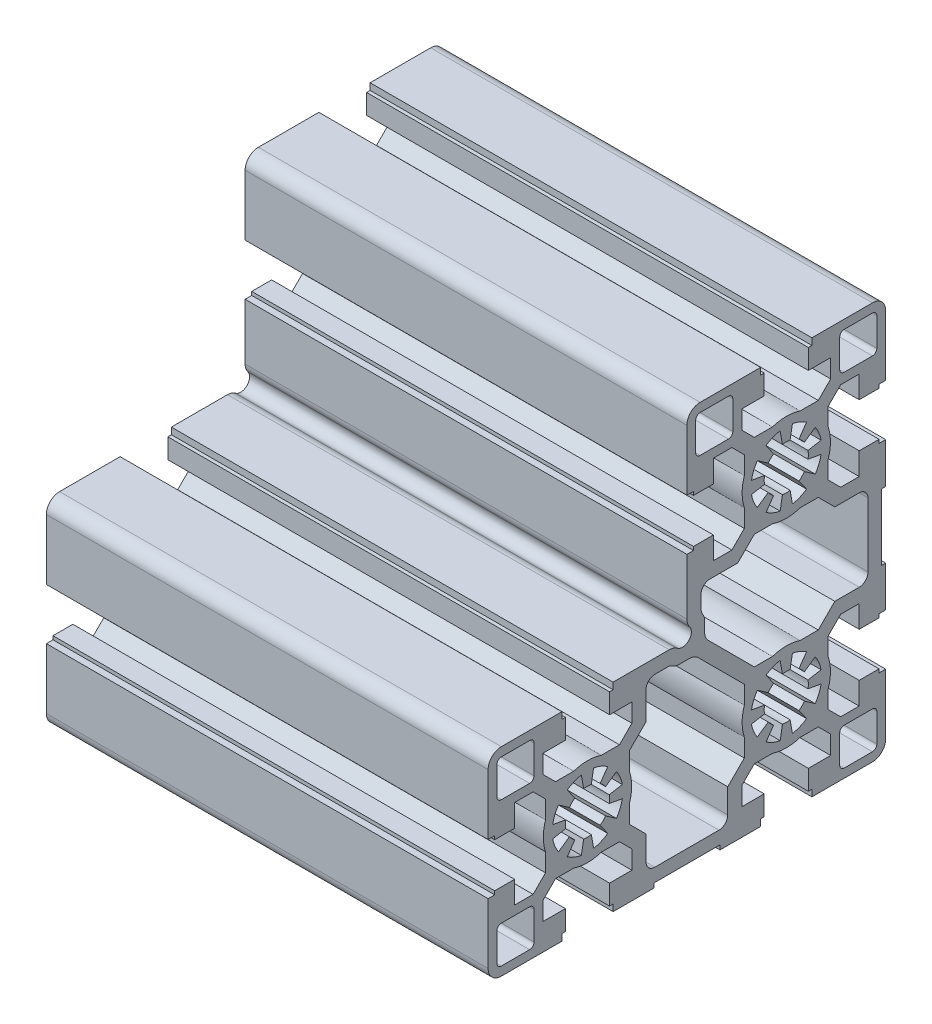
SolidWorks part; units mm, degrees
material "6063-T6"
ref_plane "Front Plane" through (0, 0, 0) normal (0, 0, 1) x (1, 0, 0)
ref_plane "Top Plane" through (0, 0, 0) normal (0, 1, 0) x (1, 0, 0)
ref_plane "Right Plane" through (0, 0, 0) normal (1, 0, 0) x (0, 0, -1)
sketch "Эскиз2" plane through (0, 0, 0) normal (1, 0, 0) x (0, 0, -1)
  point P0 (0, 0)
  line B0 (13.1, 65.5) -> (19.5, 65.5)
  line B1 (20.5, 64.5) -> (20.5, 58.1)
  line B2 (19.5, 57.1) -> (13.1, 57.1)
  line B3 (12.1, 58.1) -> (12.1, 64.5)
  line B4 (-67.5, -19.5) -> (-67.5, -5.8)
  line B5 (-67.5, 5.8) -> (-67.5, 19.5)
  line B6 (-18.7635, 25.406) -> (-19.0365, 25.8837)
  line B7 (-19.3, 26.8759) -> (-19.3, 29.7496)
  line B8 (-17.3, 31.7496) -> (-10.9877, 31.7496)
  line B9 (-10.9877, 31.7496) -> (-7.2373, 35.5)
  line B10 (-7.2373, 35.5) -> (-3.1225, 35.5)
  line B11 (3.1225, 35.5) -> (7.2373, 35.5)
  line B12 (7.2373, 35.5) -> (10.9877, 31.7496)
  line B13 (10.9877, 31.7496) -> (16.5, 31.7496)
  line B14 (18.5, 29.7496) -> (18.5, 15.25)
  line B15 (16.5, 13.25) -> (10.9873, 13.25)
  line B16 (10.9873, 13.25) -> (7.2373, 9.5)
  line B17 (7.2373, 9.5) -> (3.1225, 9.5)
  line B18 (-3.1225, 9.5) -> (-7.2373, 9.5)
  line B19 (-7.2373, 9.5) -> (-17.6213, 19.8841)
  line B20 (-18.5, 22.0054) -> (-18.5, 24.4137)
  line B21 (-7.8785, 43.6108) -> (-4.924, 44.1318)
  line B22 (-4.924, 45.8682) -> (-7.8785, 46.3892)
  line B23 (-6.5532, 49.5886) -> (-4.0958, 47.8679)
  line B24 (-2.8679, 49.0958) -> (-4.5886, 51.5532)
  line B25 (-1.3892, 52.8785) -> (-0.8682, 49.924)
  line B26 (0.8682, 49.924) -> (1.3892, 52.8785)
  line B27 (4.5886, 51.5532) -> (2.8679, 49.0958)
  line B28 (4.0958, 47.8679) -> (6.5532, 49.5886)
  line B29 (7.8785, 46.3892) -> (4.924, 45.8682)
  line B30 (4.924, 44.1318) -> (7.8785, 43.6108)
  line B31 (6.5532, 40.4114) -> (4.0958, 42.1321)
  line B32 (2.8679, 40.9042) -> (4.5886, 38.4468)
  line B33 (1.3892, 37.1215) -> (0.8682, 40.076)
  line B34 (-0.8682, 40.076) -> (-1.3892, 37.1215)
  line B35 (-4.5886, 38.4468) -> (-2.8679, 40.9042)
  line B36 (-4.0958, 42.1321) -> (-6.5532, 40.4114)
  line B37 (-39.2, 22.5) -> (-26.5033, 22.5)
  line B38 (-39.2, 21) -> (-39.2, 22.5)
  line B39 (-40, 21) -> (-39.2, 21)
  line B40 (-40, 16.5) -> (-40, 21)
  line B41 (-34.95, 16.5) -> (-40, 16.5)
  line B42 (-34.95, 12.3127) -> (-34.95, 16.5)
  line B43 (-37.7627, 9.5) -> (-34.95, 12.3127)
  line B44 (-41.8775, 9.5) -> (-37.7627, 9.5)
  line B45 (-52.2373, 9.5) -> (-48.1225, 9.5)
  line B46 (-55.05, 12.3127) -> (-52.2373, 9.5)
  line B47 (-55.05, 16.5) -> (-55.05, 12.3127)
  line B48 (-50, 16.5) -> (-55.05, 16.5)
  line B49 (-50, 21) -> (-50, 16.5)
  line B50 (-50.8, 21) -> (-50, 21)
  line B51 (-50.8, 22.5) -> (-50.8, 21)
  line B52 (-64.5, 22.5) -> (-50.8, 22.5)
  line B53 (-66, 5) -> (-66, 5.8)
  line B54 (-61.5, 5) -> (-66, 5)
  line B55 (-61.5, 10.05) -> (-61.5, 5)
  line B56 (-57.3127, 10.05) -> (-61.5, 10.05)
  line B57 (-54.5, 7.2373) -> (-57.3127, 10.05)
  line B58 (-54.5, 3.1225) -> (-54.5, 7.2373)
  line B59 (-54.5, -7.2373) -> (-54.5, -3.1225)
  line B60 (-57.3127, -10.05) -> (-54.5, -7.2373)
  line B61 (-61.5, -10.05) -> (-57.3127, -10.05)
  line B62 (-61.5, -5) -> (-61.5, -10.05)
  line B63 (-66, -5) -> (-61.5, -5)
  line B64 (-66, -5.8) -> (-66, -5)
  line B65 (-50.8, -22.5) -> (-64.5, -22.5)
  line B66 (-50.8, -21) -> (-50.8, -22.5)
  line B67 (-50, -21) -> (-50.8, -21)
  line B68 (-50, -16.5) -> (-50, -21)
  line B69 (-55.05, -16.5) -> (-50, -16.5)
  line B70 (-55.05, -12.3127) -> (-55.05, -16.5)
  line B71 (-52.2373, -9.5) -> (-55.05, -12.3127)
  line B72 (-48.1225, -9.5) -> (-52.2373, -9.5)
  line B73 (-37.7627, -9.5) -> (-41.8775, -9.5)
  line B74 (-34.95, -12.3127) -> (-37.7627, -9.5)
  line B75 (-34.95, -16.5) -> (-34.95, -12.3127)
  line B76 (-40, -16.5) -> (-34.95, -16.5)
  line B77 (-40, -21) -> (-40, -16.5)
  line B78 (-39.2, -21) -> (-40, -21)
  line B79 (-39.2, -22.5) -> (-39.2, -21)
  line B80 (-30, -22.5) -> (-39.2, -22.5)
  line B81 (-30, -21.5) -> (-30, -22.5)
  line B82 (-15, -21.5) -> (-30, -21.5)
  line B83 (-15, -22.5) -> (-15, -21.5)
  line B84 (-5.8, -22.5) -> (-15, -22.5)
  line B85 (-5.8, -21) -> (-5.8, -22.5)
  line B86 (-5, -21) -> (-5.8, -21)
  line B87 (-5, -16.5) -> (-5, -21)
  line B88 (-10.05, -16.5) -> (-5, -16.5)
  line B89 (-10.05, -12.3127) -> (-10.05, -16.5)
  line B90 (-7.2373, -9.5) -> (-10.05, -12.3127)
  line B91 (-3.1225, -9.5) -> (-7.2373, -9.5)
  line B92 (7.2373, -9.5) -> (3.1225, -9.5)
  line B93 (10.05, -12.3127) -> (7.2373, -9.5)
  line B94 (10.05, -16.5) -> (10.05, -12.3127)
  line B95 (5, -16.5) -> (10.05, -16.5)
  line B96 (5, -21) -> (5, -16.5)
  line B97 (5.8, -21) -> (5, -21)
  line B98 (5.8, -22.5) -> (5.8, -21)
  line B99 (19.5, -22.5) -> (5.8, -22.5)
  line B100 (22.5, -5.8) -> (22.5, -19.5)
  line B101 (21, -5.8) -> (22.5, -5.8)
  line B102 (21, -5) -> (21, -5.8)
  line B103 (16.5, -5) -> (21, -5)
  line B104 (16.5, -10.05) -> (16.5, -5)
  line B105 (12.3127, -10.05) -> (16.5, -10.05)
  line B106 (9.5, -7.2373) -> (12.3127, -10.05)
  line B107 (9.5, -3.1225) -> (9.5, -7.2373)
  line B108 (9.5, 7.2373) -> (9.5, 3.1225)
  line B109 (12.3127, 10.05) -> (9.5, 7.2373)
  line B110 (16.5, 10.05) -> (12.3127, 10.05)
  line B111 (16.5, 5) -> (16.5, 10.05)
  line B112 (21, 5) -> (16.5, 5)
  line B113 (21, 5.8) -> (21, 5)
  line B114 (22.5, 5.8) -> (21, 5.8)
  line B115 (22.5, 15) -> (22.5, 5.8)
  line B116 (21.5, 15) -> (22.5, 15)
  line B117 (21.5, 30) -> (21.5, 15)
  line B118 (22.5, 30) -> (21.5, 30)
  line B119 (22.5, 39.2) -> (22.5, 30)
  line B120 (21, 39.2) -> (22.5, 39.2)
  line B121 (21, 40) -> (21, 39.2)
  line B122 (16.5, 40) -> (21, 40)
  line B123 (16.5, 34.95) -> (16.5, 40)
  line B124 (12.3127, 34.95) -> (16.5, 34.95)
  line B125 (9.5, 37.7627) -> (12.3127, 34.95)
  line B126 (9.5, 41.8775) -> (9.5, 37.7627)
  line B127 (9.5, 52.2373) -> (9.5, 48.1225)
  line B128 (12.3127, 55.05) -> (9.5, 52.2373)
  line B129 (16.5, 55.05) -> (12.3127, 55.05)
  line B130 (16.5, 50) -> (16.5, 55.05)
  line B131 (21, 50) -> (16.5, 50)
  line B132 (21, 50.8) -> (21, 50)
  line B133 (22.5, 50.8) -> (21, 50.8)
  line B134 (22.5, 64.5) -> (22.5, 50.8)
  line B135 (5.8, 67.5) -> (19.5, 67.5)
  line B136 (5.8, 66) -> (5.8, 67.5)
  line B137 (5, 66) -> (5.8, 66)
  line B138 (5, 61.5) -> (5, 66)
  line B139 (10.05, 61.5) -> (5, 61.5)
  line B140 (10.05, 57.3127) -> (10.05, 61.5)
  line B141 (7.2373, 54.5) -> (10.05, 57.3127)
  line B142 (3.1225, 54.5) -> (7.2373, 54.5)
  line B143 (-7.2373, 54.5) -> (-3.1225, 54.5)
  line B144 (-10.05, 57.3127) -> (-7.2373, 54.5)
  line B145 (-10.05, 61.5) -> (-10.05, 57.3127)
  line B146 (-5, 61.5) -> (-10.05, 61.5)
  line B147 (-5, 66) -> (-5, 61.5)
  line B148 (-5.8, 66) -> (-5, 66)
  line B149 (-5.8, 67.5) -> (-5.8, 66)
  line B150 (-19.5, 67.5) -> (-5.8, 67.5)
  line B151 (-22.5, 50.8) -> (-22.5, 64.5)
  line B152 (-21, 50.8) -> (-22.5, 50.8)
  line B153 (-21, 50) -> (-21, 50.8)
  line B154 (-16.5, 50) -> (-21, 50)
  line B155 (-16.5, 55.05) -> (-16.5, 50)
  line B156 (-12.3127, 55.05) -> (-16.5, 55.05)
  line B157 (-9.5, 52.2373) -> (-12.3127, 55.05)
  line B158 (-9.5, 48.1225) -> (-9.5, 52.2373)
  line B159 (-9.5, 37.7627) -> (-9.5, 41.8775)
  line B160 (-12.3127, 34.95) -> (-9.5, 37.7627)
  line B161 (-16.5, 34.95) -> (-12.3127, 34.95)
  line B162 (-16.5, 40) -> (-16.5, 34.95)
  line B163 (-21, 40) -> (-16.5, 40)
  line B164 (-21, 39.2) -> (-21, 40)
  line B165 (-22.5, 39.2) -> (-21, 39.2)
  line B166 (-22.5, 26.5033) -> (-22.5, 39.2)
  line B167 (-20.5, 58.1) -> (-20.5, 64.5)
  line B168 (-19.5, 65.5) -> (-13.1, 65.5)
  line B169 (-12.1, 64.5) -> (-12.1, 58.1)
  line B170 (-13.1, 57.1) -> (-19.5, 57.1)
  line B171 (-57.1, 19.5) -> (-57.1, 13.1)
  line B172 (-58.1, 12.1) -> (-64.5, 12.1)
  line B173 (-65.5, 13.1) -> (-65.5, 19.5)
  line B174 (-64.5, 20.5) -> (-58.1, 20.5)
  line B175 (-52.8785, -1.3892) -> (-49.924, -0.8682)
  line B176 (-49.924, 0.8682) -> (-52.8785, 1.3892)
  line B177 (-51.5532, 4.5886) -> (-49.0958, 2.8679)
  line B178 (-47.8679, 4.0958) -> (-49.5886, 6.5532)
  line B179 (-46.3892, 7.8785) -> (-45.8682, 4.924)
  line B180 (-44.1318, 4.924) -> (-43.6108, 7.8785)
  line B181 (-40.4114, 6.5532) -> (-42.1321, 4.0958)
  line B182 (-40.9042, 2.8679) -> (-38.4468, 4.5886)
  line B183 (-37.1215, 1.3892) -> (-40.076, 0.8682)
  line B184 (-40.076, -0.8682) -> (-37.1215, -1.3892)
  line B185 (-38.4468, -4.5886) -> (-40.9042, -2.8679)
  line B186 (-42.1321, -4.0958) -> (-40.4114, -6.5532)
  line B187 (-43.6108, -7.8785) -> (-44.1318, -4.924)
  line B188 (-45.8682, -4.924) -> (-46.3892, -7.8785)
  line B189 (-49.5886, -6.5532) -> (-47.8679, -4.0958)
  line B190 (-49.0958, -2.8679) -> (-51.5532, -4.5886)
  line B191 (-19.8841, 17.6213) -> (-9.5, 7.2373)
  line B192 (-9.5, 7.2373) -> (-9.5, 3.1225)
  line B193 (-9.5, -3.1225) -> (-9.5, -7.2373)
  line B194 (-9.5, -7.2373) -> (-13.25, -10.9873)
  line B195 (-13.25, -10.9873) -> (-13.25, -16.5)
  line B196 (-15.25, -18.5) -> (-29.7496, -18.5)
  line B197 (-31.7496, -16.5) -> (-31.7496, -10.9877)
  line B198 (-31.7496, -10.9877) -> (-35.5, -7.2373)
  line B199 (-35.5, -7.2373) -> (-35.5, -3.1225)
  line B200 (-35.5, 3.1225) -> (-35.5, 7.2373)
  line B201 (-35.5, 7.2373) -> (-31.7496, 10.9877)
  line B202 (-31.7496, 10.9877) -> (-31.7496, 17.3)
  line B203 (-29.7496, 19.3) -> (-26.8759, 19.3)
  line B204 (-25.8837, 19.0365) -> (-25.406, 18.7635)
  line B205 (-24.4137, 18.5) -> (-22.0054, 18.5)
  line B206 (-7.8785, -1.3892) -> (-4.924, -0.8682)
  line B207 (-4.924, 0.8682) -> (-7.8785, 1.3892)
  line B208 (-6.5532, 4.5886) -> (-4.0958, 2.8679)
  line B209 (-2.8679, 4.0958) -> (-4.5886, 6.5532)
  line B210 (-1.3892, 7.8785) -> (-0.8682, 4.924)
  line B211 (0.8682, 4.924) -> (1.3892, 7.8785)
  line B212 (4.5886, 6.5532) -> (2.8679, 4.0958)
  line B213 (4.0958, 2.8679) -> (6.5532, 4.5886)
  line B214 (7.8785, 1.3892) -> (4.924, 0.8682)
  line B215 (4.924, -0.8682) -> (7.8785, -1.3892)
  line B216 (6.5532, -4.5886) -> (4.0958, -2.8679)
  line B217 (2.8679, -4.0958) -> (4.5886, -6.5532)
  line B218 (1.3892, -7.8785) -> (0.8682, -4.924)
  line B219 (-0.8682, -4.924) -> (-1.3892, -7.8785)
  line B220 (-4.5886, -6.5532) -> (-2.8679, -4.0958)
  line B221 (-4.0958, -2.8679) -> (-6.5532, -4.5886)
  line B222 (-58.1, -20.5) -> (-64.5, -20.5)
  line B223 (-65.5, -19.5) -> (-65.5, -13.1)
  line B224 (-64.5, -12.1) -> (-58.1, -12.1)
  line B225 (-57.1, -13.1) -> (-57.1, -19.5)
  line B226 (20.5, -13.1) -> (20.5, -19.5)
  line B227 (19.5, -20.5) -> (13.1, -20.5)
  line B228 (12.1, -19.5) -> (12.1, -13.1)
  line B229 (13.1, -12.1) -> (19.5, -12.1)
  line B230 (-67.5, -5.8) -> (-66, -5.8)
  line B231 (-66, 5.8) -> (-67.5, 5.8)
  arc B232 (12.1, 64.5) -> (13.1, 65.5) centre (13.1, 64.5) cw
  arc B233 (19.5, 65.5) -> (20.5, 64.5) centre (19.5, 64.5) cw
  arc B234 (20.5, 58.1) -> (19.5, 57.1) centre (19.5, 58.1) cw
  arc B235 (13.1, 57.1) -> (12.1, 58.1) centre (13.1, 58.1) cw
  arc B236 (-20.5, 64.5) -> (-19.5, 65.5) centre (-19.5, 64.5) cw
  arc B237 (-13.1, 65.5) -> (-12.1, 64.5) centre (-13.1, 64.5) cw
  arc B238 (-12.1, 58.1) -> (-13.1, 57.1) centre (-13.1, 58.1) cw
  arc B239 (-19.5, 57.1) -> (-20.5, 58.1) centre (-19.5, 58.1) cw
  arc B240 (-18.7635, 25.406) -> (-18.5, 24.4137) centre (-20.5, 24.4137) cw
  arc B241 (-19.0365, 25.8837) -> (-19.3, 26.8759) centre (-17.3, 26.8759) cw
  arc B242 (-19.3, 29.7496) -> (-17.3, 31.7496) centre (-17.3, 29.7496) cw
  arc B243 (3.1225, 35.5) -> (-3.1225, 35.5) centre (0, 45) cw
  arc B244 (16.5, 31.7496) -> (18.5, 29.7496) centre (16.5, 29.7496) cw
  arc B245 (18.5, 15.25) -> (16.5, 13.25) centre (16.5, 15.25) cw
  arc B246 (-3.1225, 9.5) -> (3.1225, 9.5) centre (0, 0) cw
  arc B247 (-17.6213, 19.8841) -> (-18.5, 22.0054) centre (-15.5, 22.0054) cw
  arc B248 (-6.5532, 40.4114) -> (-7.8785, 43.6108) centre (0, 45) cw
  arc B249 (-4.924, 44.1318) -> (-4.924, 45.8682) centre (0, 45) cw
  arc B250 (-7.8785, 46.3892) -> (-6.5532, 49.5886) centre (0, 45) cw
  arc B251 (-4.0958, 47.8679) -> (-2.8679, 49.0958) centre (0, 45) cw
  arc B252 (-4.5886, 51.5532) -> (-1.3892, 52.8785) centre (0, 45) cw
  arc B253 (-0.8682, 49.924) -> (0.8682, 49.924) centre (0, 45) cw
  arc B254 (1.3892, 52.8785) -> (4.5886, 51.5532) centre (0, 45) cw
  arc B255 (2.8679, 49.0958) -> (4.0958, 47.8679) centre (0, 45) cw
  arc B256 (6.5532, 49.5886) -> (7.8785, 46.3892) centre (0, 45) cw
  arc B257 (4.924, 45.8682) -> (4.924, 44.1318) centre (0, 45) cw
  arc B258 (7.8785, 43.6108) -> (6.5532, 40.4114) centre (0, 45) cw
  arc B259 (4.0958, 42.1321) -> (2.8679, 40.9042) centre (0, 45) cw
  arc B260 (4.5886, 38.4468) -> (1.3892, 37.1215) centre (0, 45) cw
  arc B261 (0.8682, 40.076) -> (-0.8682, 40.076) centre (0, 45) cw
  arc B262 (-1.3892, 37.1215) -> (-4.5886, 38.4468) centre (0, 45) cw
  arc B263 (-2.8679, 40.9042) -> (-4.0958, 42.1321) centre (0, 45) cw
  arc B264 (-57.1, 13.1) -> (-58.1, 12.1) centre (-58.1, 13.1) cw
  arc B265 (-64.5, 12.1) -> (-65.5, 13.1) centre (-64.5, 13.1) cw
  arc B266 (-65.5, 19.5) -> (-64.5, 20.5) centre (-64.5, 19.5) cw
  arc B267 (-58.1, 20.5) -> (-57.1, 19.5) centre (-58.1, 19.5) cw
  arc B268 (-51.5532, -4.5886) -> (-52.8785, -1.3892) centre (-45, 0) cw
  arc B269 (-49.924, -0.8682) -> (-49.924, 0.8682) centre (-45, 0) cw
  arc B270 (-52.8785, 1.3892) -> (-51.5532, 4.5886) centre (-45, 0) cw
  arc B271 (-49.0958, 2.8679) -> (-47.8679, 4.0958) centre (-45, 0) cw
  arc B272 (-49.5886, 6.5532) -> (-46.3892, 7.8785) centre (-45, 0) cw
  arc B273 (-45.8682, 4.924) -> (-44.1318, 4.924) centre (-45, 0) cw
  arc B274 (-43.6108, 7.8785) -> (-40.4114, 6.5532) centre (-45, 0) cw
  arc B275 (-42.1321, 4.0958) -> (-40.9042, 2.8679) centre (-45, 0) cw
  arc B276 (-38.4468, 4.5886) -> (-37.1215, 1.3892) centre (-45, 0) cw
  arc B277 (-40.076, 0.8682) -> (-40.076, -0.8682) centre (-45, 0) cw
  arc B278 (-37.1215, -1.3892) -> (-38.4468, -4.5886) centre (-45, 0) cw
  arc B279 (-40.9042, -2.8679) -> (-42.1321, -4.0958) centre (-45, 0) cw
  arc B280 (-40.4114, -6.5532) -> (-43.6108, -7.8785) centre (-45, 0) cw
  arc B281 (-44.1318, -4.924) -> (-45.8682, -4.924) centre (-45, 0) cw
  arc B282 (-46.3892, -7.8785) -> (-49.5886, -6.5532) centre (-45, 0) cw
  arc B283 (-47.8679, -4.0958) -> (-49.0958, -2.8679) centre (-45, 0) cw
  arc B284 (-57.1, -19.5) -> (-58.1, -20.5) centre (-58.1, -19.5) cw
  arc B285 (-64.5, -20.5) -> (-65.5, -19.5) centre (-64.5, -19.5) cw
  arc B286 (-65.5, -13.1) -> (-64.5, -12.1) centre (-64.5, -13.1) cw
  arc B287 (-58.1, -12.1) -> (-57.1, -13.1) centre (-58.1, -13.1) cw
  arc B288 (-22.0054, 18.5) -> (-19.8841, 17.6213) centre (-22.0054, 15.5) cw
  arc B289 (-9.5, -3.1225) -> (-9.5, 3.1225) centre (0, 0) cw
  arc B290 (-13.25, -16.5) -> (-15.25, -18.5) centre (-15.25, -16.5) cw
  arc B291 (-29.7496, -18.5) -> (-31.7496, -16.5) centre (-29.7496, -16.5) cw
  arc B292 (-35.5, 3.1225) -> (-35.5, -3.1225) centre (-45, 0) cw
  arc B293 (-31.7496, 17.3) -> (-29.7496, 19.3) centre (-29.7496, 17.3) cw
  arc B294 (-26.8759, 19.3) -> (-25.8837, 19.0365) centre (-26.8759, 17.3) cw
  arc B295 (-24.4137, 18.5) -> (-25.406, 18.7635) centre (-24.4137, 20.5) cw
  arc B296 (-6.5532, -4.5886) -> (-7.8785, -1.3892) centre (0, 0) cw
  arc B297 (-4.924, -0.8682) -> (-4.924, 0.8682) centre (0, 0) cw
  arc B298 (-7.8785, 1.3892) -> (-6.5532, 4.5886) centre (0, 0) cw
  arc B299 (-4.0958, 2.8679) -> (-2.8679, 4.0958) centre (0, 0) cw
  arc B300 (-4.5886, 6.5532) -> (-1.3892, 7.8785) centre (0, 0) cw
  arc B301 (-0.8682, 4.924) -> (0.8682, 4.924) centre (0, 0) cw
  arc B302 (1.3892, 7.8785) -> (4.5886, 6.5532) centre (0, 0) cw
  arc B303 (2.8679, 4.0958) -> (4.0958, 2.8679) centre (0, 0) cw
  arc B304 (6.5532, 4.5886) -> (7.8785, 1.3892) centre (0, 0) cw
  arc B305 (4.924, 0.8682) -> (4.924, -0.8682) centre (0, 0) cw
  arc B306 (7.8785, -1.3892) -> (6.5532, -4.5886) centre (0, 0) cw
  arc B307 (4.0958, -2.8679) -> (2.8679, -4.0958) centre (0, 0) cw
  arc B308 (4.5886, -6.5532) -> (1.3892, -7.8785) centre (0, 0) cw
  arc B309 (0.8682, -4.924) -> (-0.8682, -4.924) centre (0, 0) cw
  arc B310 (-1.3892, -7.8785) -> (-4.5886, -6.5532) centre (0, 0) cw
  arc B311 (-2.8679, -4.0958) -> (-4.0958, -2.8679) centre (0, 0) cw
  arc B312 (-21.894, 24.6953) -> (-24.6953, 21.894) centre (-23.4899, 23.4899) cw
  arc B313 (-26.5033, 22.5) -> (-24.6953, 21.894) centre (-26.5033, 19.5) cw
  arc B314 (-48.1225, 9.5) -> (-41.8775, 9.5) centre (-45, 0) cw
  arc B315 (-67.5, 19.5) -> (-64.5, 22.5) centre (-64.5, 19.5) cw
  arc B316 (-54.5, -3.1225) -> (-54.5, 3.1225) centre (-45, 0) cw
  arc B317 (-64.5, -22.5) -> (-67.5, -19.5) centre (-64.5, -19.5) cw
  arc B318 (-41.8775, -9.5) -> (-48.1225, -9.5) centre (-45, 0) cw
  arc B319 (3.1225, -9.5) -> (-3.1225, -9.5) centre (0, 0) cw
  arc B320 (22.5, -19.5) -> (19.5, -22.5) centre (19.5, -19.5) cw
  arc B321 (9.5, 3.1225) -> (9.5, -3.1225) centre (0, 0) cw
  arc B322 (9.5, 48.1225) -> (9.5, 41.8775) centre (0, 45) cw
  arc B323 (19.5, 67.5) -> (22.5, 64.5) centre (19.5, 64.5) cw
  arc B324 (-3.1225, 54.5) -> (3.1225, 54.5) centre (0, 45) cw
  arc B325 (-22.5, 64.5) -> (-19.5, 67.5) centre (-19.5, 64.5) cw
  arc B326 (-9.5, 41.8775) -> (-9.5, 48.1225) centre (0, 45) cw
  arc B327 (-21.894, 24.6953) -> (-22.5, 26.5033) centre (-19.5, 26.5033) cw
  arc B328 (19.5, -12.1) -> (20.5, -13.1) centre (19.5, -13.1) cw
  arc B329 (20.5, -19.5) -> (19.5, -20.5) centre (19.5, -19.5) cw
  arc B330 (13.1, -20.5) -> (12.1, -19.5) centre (13.1, -19.5) cw
  arc B331 (12.1, -13.1) -> (13.1, -12.1) centre (13.1, -13.1) cw
sketch_block_instance "Блок1-2"
sketch_block "Блок1"
extrude "Бобышка-Вытянуть1" add sketch "Эскиз2" against normal blind 100
